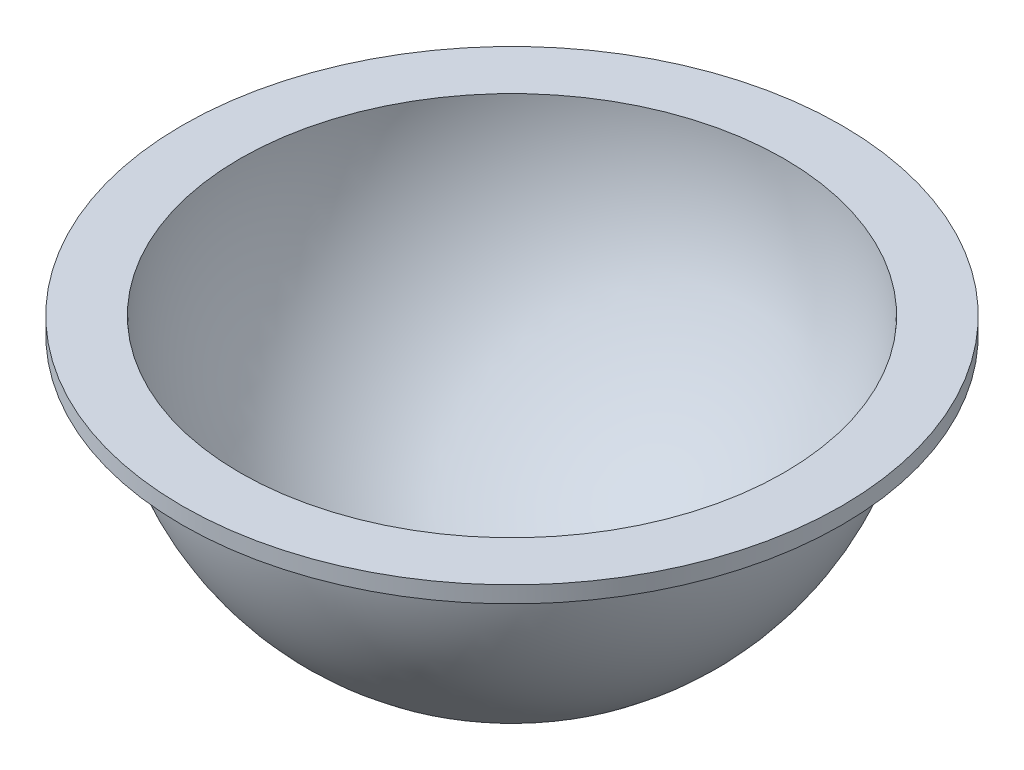
SolidWorks part; units mm, degrees
ref_plane "前视基准面" through (0, 0, 0) normal (0, 0, 1) x (1, 0, 0)
ref_plane "上视基准面" through (0, 0, 0) normal (0, 1, 0) x (1, 0, 0)
ref_plane "右视基准面" through (0, 0, 0) normal (1, 0, 0) x (0, 0, -1)
other "Configuration Table"
sketch "草图1" plane through (0, 0, 0) normal (0, 0, 1) x (1, 0, 0)
  line L0 (0, 70) -> (0, -70)
  arc A0 (0, -70) -> (0, 70) centre (0, 0) ccw
  dimension "D1" = 140
revolve "旋转1" add sketch "草图1" angle 360 about L0
sketch "草图2" plane through (0, 0, 0) normal (0, 1, 0) x (1, 0, 0)
  line L1 (-75, -75) -> (75, -75)
  line L2 (-75, -75) -> (-75, 75)
  line L3 (-75, 75) -> (75, 75)
  line L4 (75, -75) -> (75, 75)
  line L5 (-75, -75) -> (75, 75) construction
  line L6 (-75, 75) -> (75, -75) construction
  point P0 (0, 0)
  dimension "D1" = 150
extrude "切除-拉伸1" cut sketch "草图2" along normal blind 70
shell "抽壳1" thickness 4
sketch "草图3" plane through (0, 0, 0) normal (0, 1, 0) x (1, 0, 0)
  circle A0 centre (0, 0) radius 80
  circle A1 centre (0, 0) radius 70 construction
  circle A2 centre (0, 0) radius 66 construction
  circle A3 centre (0, 0) radius 66
  dimension "D1" = 10
extrude "凸台-拉伸1" add sketch "草图3" against normal blind 4
